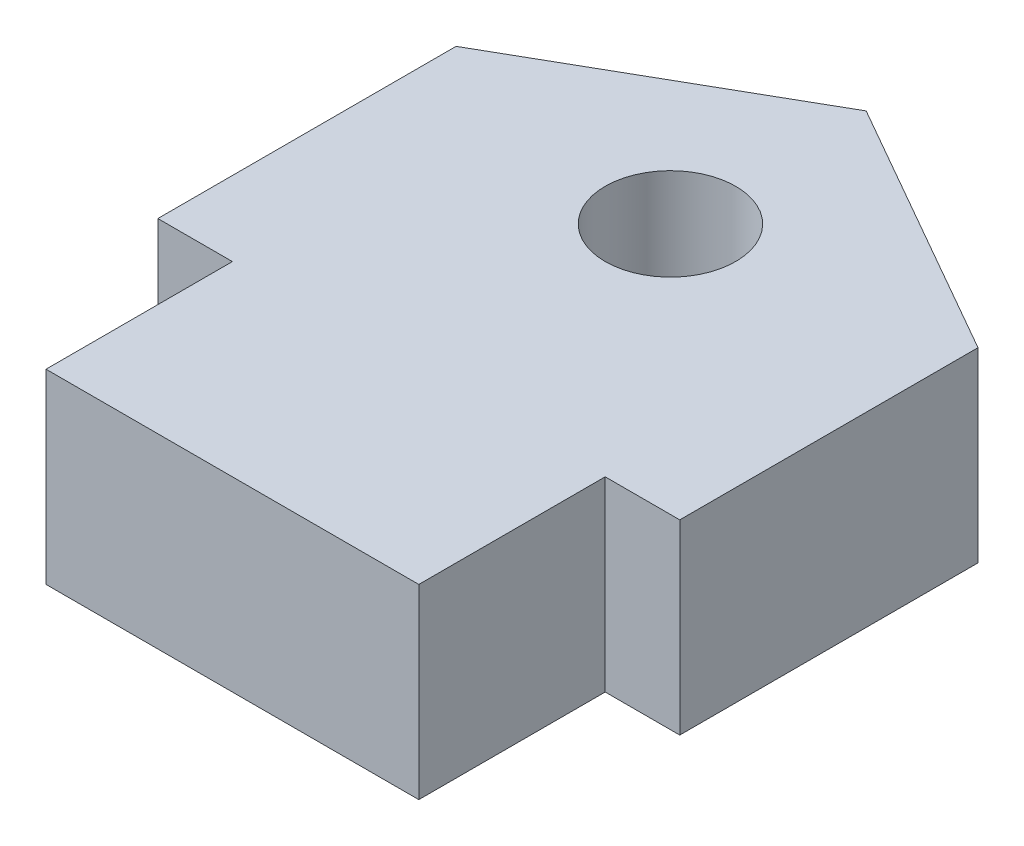
SolidWorks part; units mm, degrees
ref_plane "Front Plane" through (0, 0, 0) normal (0, 0, 1) x (1, 0, 0)
ref_plane "Top Plane" through (0, 0, 0) normal (0, 1, 0) x (1, 0, 0)
ref_plane "Right Plane" through (0, 0, 0) normal (1, 0, 0) x (0, 0, -1)
sketch "Sketch2" plane through (0, 0, 0) normal (0, 1, 0) x (1, 0, 0)
  line L2 (-214, -48.75) -> (-207, -44.75)
  line L3 (-207, -44.75) -> (-200, -48.75)
  line L5 (-200, -56.75) -> (-202, -56.75)
  line L6 (-212, -56.75) -> (-212, -61.75)
  line L7 (-212, -61.75) -> (-202, -61.75)
  line L8 (-202, -61.75) -> (-202, -56.75)
  line L9 (-212, -56.75) -> (-214, -56.75)
  line L10 (-214, -56.75) -> (-214, -48.75)
  line L11 (-234, -23.478) -> (-234, -61.4421) construction
  line L17 (-268, -48.75) -> (-268, -56.75) construction
  line L18 (-261, -44.75) -> (-268, -48.75) construction
  line L19 (-254, -48.75) -> (-261, -44.75) construction
  line L20 (-254, -56.75) -> (-254, -48.75) construction
  line L21 (-268, -56.75) -> (-254, -56.75) construction
  line L22 (-200, -48.75) -> (-200, -56.75)
  circle A0 centre (-207, -50) radius 1.75
  circle A1 centre (-261, -50) radius 1.75 construction
  point P12 (-207, -61.75)
  dimension "D8" = 3.5
  dimension "D1" = 10
  dimension "D2" = 5
  dimension "D3" = 2
  dimension "D4" = 4
  dimension "D5" = 8
  dimension "D6" = 8
  dimension "D7" = 6.75
  dimension "D9" = 202
  dimension "D10" = 50
  dimension "D11" = 20
extrude "Boss-Extrude3" add sketch "Sketch2" along normal blind 5 separate body
